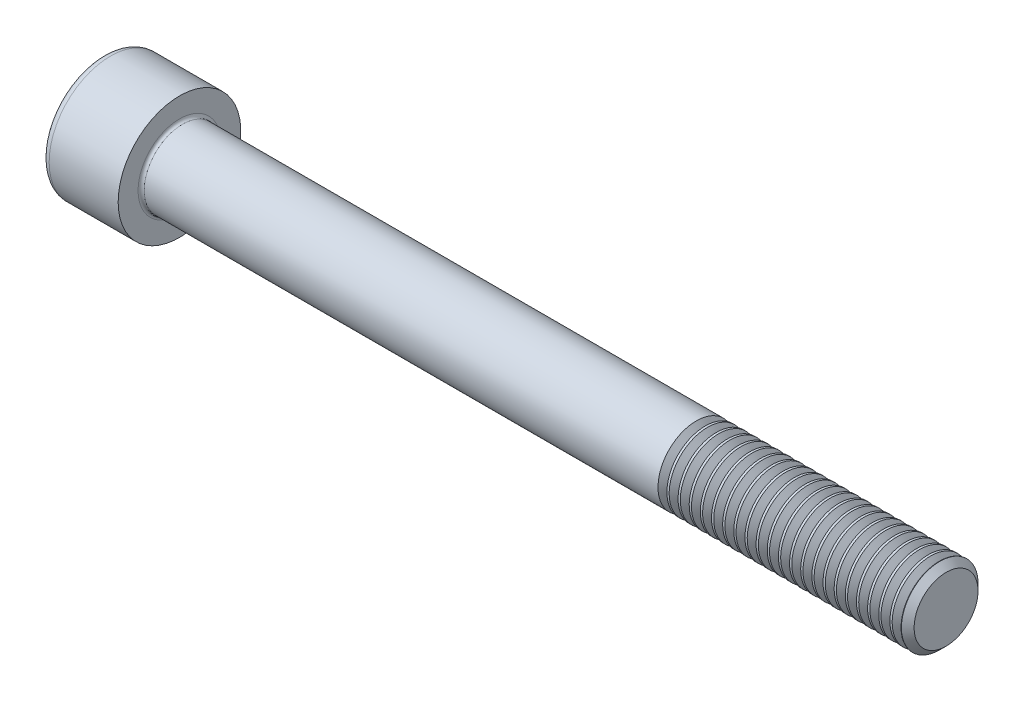
SolidWorks part; units mm, degrees
revolve "Base-Revolve" add sketch "BodySke"
sketch "BodySke" plane through (0, 0, 0) normal (0, 0, 1) x (1, 0, 0)
  line L0 (0, 0) -> (0, 8)
  line L1 (0, 8) -> (10, 8)
  line L2 (10, 8) -> (10, 5)
  line L3 (10, 5) -> (109.172, 5)
  line L4 (110, 4.172) -> (110, 0)
  line L5 (110, 0) -> (0, 0)
  line L6 (-31.75, 0) -> (127, 0) construction
  line L8 (110, 4.172) -> (109.172, 5)
  line L10 (110, -4.172) -> (109.172, -5) construction
  line L11 (11.5, 9.525) -> (11.5, 3.175) construction
  line L12 (78, 9.525) -> (78, 3.175) construction
  line L13 (50, 9.525) -> (50, 3.175) construction
  dimension "Head_ht" = 10
  dimension "Length" = 100
  dimension "Body_ch_ang" = 45
  dimension "Diameter" = 10
  dimension "Minor_dia" = 8.344
  dimension "Advance" = 1.5
  dimension "Thread_nom" = 32
  dimension "Thread_length" = 60
  dimension "Head_dia" = 16
cosmetic thread "ThreadCosmetic" [suppressed]
fillet "Fillet1" radius 0.4 1 edges at (10, 0, 5)
fillet "Fillet2" radius 1 1 edges at (0, 0, 8)
ref_plane "Plane1" through (0, 0, 0) normal (0, 0, 1) x (1, 0, 0)
ref_plane "Plane2" through (0, 0, 0) normal (0, 1, 0) x (1, 0, 0)
ref_plane "Plane3" through (0, 0, 0) normal (1, 0, 0) x (0, 0, -1)
other "Configuration Table"
sketch "Sketch2" plane through (0, 0, 0) normal (0, 0, 1) x (1, 0, 0)
  line L0 (0, 4.0125) -> (5, 4.0125)
  line L1 (5, 4.0125) -> (7.3166, 0)
  line L2 (-31.75, 0) -> (127, 0) construction
  line L3 (7.3166, 0) -> (0, 0)
  line L4 (0, 0) -> (0, 4.0125)
  line L6 (0, 0) -> (47.625, 0) construction
  dimension "D1" = 4.0125
  dimension "D2" = 60
  dimension "Depth" = 5
revolve "Hex-PreBroach" cut sketch "Sketch2" angle 360 about L6
sketch "Sketch3" plane through (0, 0, 0) normal (-1, 0, 0) x (0, 0.5, 0.866)
  line L0 (2.3166, 4.0125) -> (-2.3166, 4.0125)
  line L1 (-2.3166, 4.0125) -> (-4.6332, 0)
  line L2 (2.3166, 4.0125) -> (4.6332, 0)
  line L3 (2.3166, -4.0125) -> (4.6332, 0)
  line L4 (2.3166, -4.0125) -> (-2.3166, -4.0125)
  line L5 (-2.3166, -4.0125) -> (-4.6332, 0)
  dimension "D1" = 4.0125
  dimension "D2" = 4.0125
  dimension "Hex_size" = 8.025
extrude "Hex" cut sketch "Sketch3" against normal blind 5
sketch "ThdSchSke" plane through (0, 0, 0) normal (0, 0, 1) x (1, 0, 0)
  line L0 (78, -4.172) -> (77.4202, -5)
  line L1 (78, -4.172) -> (78.5798, -5)
  line L2 (78.5798, -5) -> (78.5798, -6.25)
  line L3 (-3.175, 0) -> (5.1513, 0) construction
  line L4 (0, 7) -> (0, -7) construction
  line L5 (78.5798, -6.25) -> (77.4202, -6.25)
  line L6 (77.4202, -6.25) -> (77.4202, -5)
  dimension "Thread_minor" = 8.344
  dimension "Diameter" = 10
  dimension "Start" = 78
revolve "ThreadSchematic" cut sketch "ThdSchSke" angle 360 about L3
pattern_linear "ThdSchPat" count 22 spacing 1.4545 along (1, 0, 0) of "ThreadSchematic"
equation "\"D2@Sketch3\" = \"Hex_size@Sketch3\" / 2"
equation "\"D1@Sketch3\" = \"Hex_size@Sketch3\" / 2"
equation "\"D1@Sketch2\" = \"Hex_size@Sketch3\" / 2"
equation "\"Thread_minor@ThreadCosmetic\"  =  \"Minor_dia@BodySke\""
equation "\"Depth@Sketch2\" =  \"Key_eng@Hex\""
equation "\"Thread_length@ThreadCosmetic\" = ((sgn( (\"Length@BodySke\" - \"Advance@BodySke\" * 3.0) - \"Thread_nom@BodySke\" )-1)*( (\"Length@BodySke\" - \"Advance@BodySke\" * 3.0) - \"Thread_nom@BodySke\" ))/-2+ \"Thread_nom@BodySke\""
equation "\"Thread_minor@ThdSchSke\" = \"Minor_dia@BodySke\""
equation "\"Diameter@ThdSchSke\" = \"Diameter@BodySke\""
equation "\"Overcut@ThdSchSke\" = \"Diameter@BodySke\" * 1.25"
equation "\"Start@ThdSchSke\" = \"Head_ht@BodySke\" + \"Length@BodySke\" - \"Thread_length@ThreadCosmetic\"  '---Non-countersunk---"
equation "\"Num_threads@ThdSchPat\" = int( \"Thread_length@ThreadCosmetic\" / \"Advance@BodySke\" + 0.999 )  + 1"
equation "\"Advance@ThdSchPat\" = \"Thread_length@ThreadCosmetic\" /  (\"Num_threads@ThdSchPat\" - 1) 'relax it"
equation "\"Num_threads@ThdSchPat\" = \"Num_threads@ThdSchPat\" - sgn( \"Num_threads@ThdSchPat\" - 1) '---chamfered tips only---"
